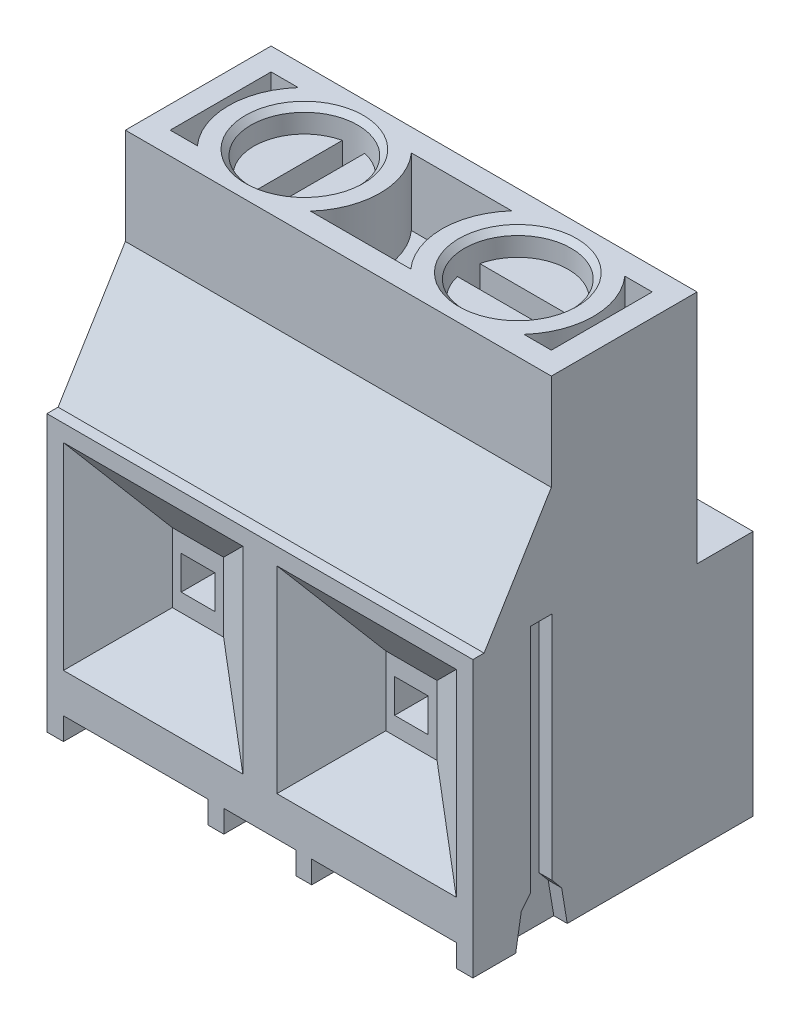
SolidWorks part; units mm, degrees
ref_plane "Front Plane" through (0, 0, 0) normal (0, 0, 1) x (1, 0, 0)
ref_plane "Top Plane" through (0, 0, 0) normal (0, 1, 0) x (1, 0, 0)
ref_plane "Right Plane" through (0, 0, 0) normal (1, 0, 0) x (0, 0, -1)
sketch "Sketch1" plane through (0, 0, 0) normal (1, 0, 0) x (0, 0, -1)
  line L0 (0, 0) -> (0, 12.3)
  line L1 (0, 12.3) -> (0.5, 12.3)
  line L2 (0.5, 12.3) -> (3.5, 17.2)
  line L3 (3.5, 17.2) -> (3.5, 21.5)
  line L4 (3.5, 21.5) -> (10, 21.5)
  line L5 (10, 21.5) -> (10, 11)
  line L6 (12.5, 0) -> (0, 0)
  line L8 (12.5, 0) -> (12.5, 11)
  line L9 (12.5, 11) -> (10, 11)
  dimension "D1" = 10
  dimension "D2" = 11
  dimension "D3" = 6.5
  dimension "D4" = 4.3
  dimension "D5" = 12.3
  dimension "D6" = 0.5
  dimension "D7" = 12.5
  dimension "D8" = 148.523
extrude "Boss-Extrude1" add sketch "Sketch1" along normal blind 19
sketch "Sketch2" plane through (0, 21.5, 0) normal (0, 1, 0) x (1, 0, 0)
  line L0 (-3.2112, 6.75) -> (22.2112, 6.75) construction
  line L1 (4.735, 11.5483) -> (4.735, 1.9517) construction
  line L2 (14.255, 11.5483) -> (14.255, 1.9517) construction
  line L3 (19, 10) -> (0, 10) construction
  line L4 (19, 3.5) -> (0, 3.5) construction
  line L5 (9.5, 11.5483) -> (9.5, 1.9517) construction
  line L6 (0, 10) -> (0, 3.5) construction
  line L7 (19, 10) -> (19, 3.5) construction
  line L12 (16.7773, 4.5) -> (18, 4.5)
  line L13 (11.7327, 9) -> (7.2573, 9)
  line L15 (7.2573, 4.5) -> (11.7327, 4.5)
  line L16 (1, 9) -> (1, 4.5)
  line L17 (1, 4.5) -> (18, 4.5)
  line L18 (18, 4.5) -> (18, 9)
  line L19 (18, 9) -> (1, 9)
  line L20 (1, 9) -> (1, 4.5)
  line L21 (1, 4.5) -> (2.2127, 4.5)
  line L22 (18, 4.5) -> (18, 9)
  line L23 (18, 9) -> (16.7773, 9)
  line L24 (2.2127, 9) -> (1, 9)
  circle A0 centre (4.735, 6.75) radius 2.38
  circle A1 centre (14.255, 6.75) radius 2.38
  arc A2 (2.2127, 9) -> (2.2127, 4.5) centre (4.735, 6.75) ccw
  arc A3 (11.7327, 9) -> (11.7327, 4.5) centre (14.255, 6.75) ccw
  circle A4 centre (4.735, 6.75) radius 3.38 construction
  circle A5 centre (14.255, 6.75) radius 3.38 construction
  arc A6 (7.2573, 4.5) -> (7.2573, 9) centre (4.735, 6.75) ccw
  arc A7 (16.7773, 4.5) -> (16.7773, 9) centre (14.255, 6.75) ccw
  point P3 (9.5, 6.75)
  point P6 (4.735, 6.75)
  point P9 (14.255, 6.75)
  point P16 (9.5, 6.75)
  dimension "D3" = 4.76
  dimension "D4" = 1
  dimension "D1" = 9.52
  dimension "D2" = 4.765
  dimension "D5" = 1
  dimension "D6" = 1
extrude "Cut-Extrude1" cut sketch "Sketch2" against normal blind 3
sketch "Sketch3" plane through (19, 0, 0) normal (1, 0, 0) x (0, 0, -1)
  line L0 (3.06, 0) -> (3.06, 6.7436) construction
  line L2 (0, 0) -> (12.5, 0) construction
  line L3 (1.91, 0) -> (2.16, 1.5)
  line L4 (2.16, 1.5) -> (2.58, 2)
  line L5 (2.58, 2) -> (2.58, 12.3)
  line L6 (2.58, 12.3) -> (3.54, 12.3)
  line L7 (1.91, 0) -> (4.21, 0)
  line L8 (0.5, 12.3) -> (0, 12.3) construction
  line L9 (0, 12.3) -> (0, 0) construction
  line L10 (3.54, 2) -> (3.54, 12.3)
  line L11 (3.96, 1.5) -> (3.54, 2)
  line L12 (4.21, 0) -> (3.96, 1.5)
  point P14 (3.06, 12.3)
  dimension "D1" = 1.15
  dimension "D2" = 0.9
  dimension "D3" = 0.48
  dimension "D4" = 2.58
  dimension "D5" = 1.5
  dimension "D6" = 0.5
extrude "Cut-Extrude2" cut sketch "Sketch3" against normal blind 0.6
sketch "Sketch4" plane through (0, 0, 0) normal (-1, 0, 0) x (0, 0, 1)
  line L0 (-1.91, 0) -> (-4.21, 0) construction
  line L1 (-3.54, 12.3) -> (-2.58, 12.3)
  line L2 (-3.54, 12.3) -> (-3.54, 0)
  line L3 (-3.54, 0) -> (-2.58, 0)
  line L4 (-2.58, 12.3) -> (-2.58, 0)
extrude "Boss-Extrude2" add sketch "Sketch4" along normal blind 0.6
chamfer "Chamfer1" distance 0.25 angle 45 2 edges at (4.735, 21.5, -4.37) (14.255, 21.5, -4.37)
sketch "Sketch6" plane through (0, 18.5, 0) normal (0, 1, 0) x (1, 0, 0)
  circle A0 centre (14.255, 6.75) radius 2.25
  circle A1 centre (4.735, 6.75) radius 2.25
  dimension "D1" = 4.5
extrude "Boss-Extrude3" add sketch "Sketch6" along normal blind 2 separate body
sketch "Sketch7" plane through (0, 20.5, 0) normal (0, 1, 0) x (1, 0, 0)
  line L2 (4.235, 8.9437) -> (4.235, 4.5563)
  line L4 (5.235, 8.9437) -> (5.235, 4.5563)
  line L7 (12.0613, 7.25) -> (16.4487, 7.25)
  line L9 (12.0613, 6.25) -> (16.4487, 6.25)
  circle A0 centre (4.735, 6.75) radius 2.25 construction
  circle A1 centre (14.255, 6.75) radius 2.25
  arc A2 (12.0613, 7.25) -> (12.0613, 6.25) centre (14.255, 6.75) ccw
  arc A3 (5.235, 8.9437) -> (4.235, 8.9437) centre (4.735, 6.75) ccw
  arc A5 (16.4487, 6.25) -> (16.4487, 7.25) centre (14.255, 6.75) ccw
  arc A6 (4.235, 4.5563) -> (5.235, 4.5563) centre (4.735, 6.75) ccw
  dimension "D1" = 0
extrude "Cut-Extrude3" cut sketch "Sketch7" against normal blind 1
sketch "Sketch8" plane through (0, 0, 0) normal (0, 0, 1) x (1, 0, 0)
  line L0 (4.74, 13.0511) -> (4.74, -1.0842) construction
  line L1 (9.5, 27.1864) -> (9.5, -1.0842) construction
  line L2 (14.26, 15.3842) -> (14.26, -1.0842) construction
  line L3 (0, 12.3) -> (0, 0) construction
  line L4 (19, 2) -> (19, 12.3) construction
  line L5 (19, 12.3) -> (0, 12.3) construction
  line L6 (10.26, 11.55) -> (18.26, 11.55)
  line L7 (10.26, 11.55) -> (10.26, 2.75)
  line L8 (10.26, 2.75) -> (18.26, 2.75)
  line L9 (18.26, 11.55) -> (18.26, 2.75)
  line L10 (10.26, 11.55) -> (18.26, 2.75) construction
  line L11 (10.26, 2.75) -> (18.26, 11.55) construction
  line L13 (0.74, 11.55) -> (8.74, 11.55)
  line L14 (0.74, 11.55) -> (0.74, 2.75)
  line L15 (0.74, 2.75) -> (8.74, 2.75)
  line L16 (8.74, 11.55) -> (8.74, 2.75)
  line L17 (0.74, 11.55) -> (8.74, 2.75) construction
  line L18 (0.74, 2.75) -> (8.74, 11.55) construction
  point P3 (4.74, 5.9835)
  point P6 (9.5, 13.0511)
  point P7 (14.26, 7.15)
  point P9 (15.9184, 13.0511)
  point P14 (14.26, 7.15)
  point P21 (4.74, 7.15)
  dimension "D1" = 9.52
  dimension "D2" = 4.76
  dimension "D3" = 8.8
  dimension "D4" = 8
  dimension "D5" = 0.75
  dimension "D6" = 8.8
  dimension "D7" = 8
extrude "Cut-Extrude4" cut sketch "Sketch8" against normal blind 2 draft 55
sketch "Sketch9" plane through (0, 0, -2) normal (0, 0, 1) x (1, 0, 0)
  line L1 (3.99, 7.9) -> (5.49, 7.9)
  line L2 (3.99, 7.9) -> (3.99, 6.4)
  line L3 (3.99, 6.4) -> (5.49, 6.4)
  line L4 (5.49, 7.9) -> (5.49, 6.4)
  line L5 (3.99, 7.9) -> (5.49, 6.4) construction
  line L6 (3.99, 6.4) -> (5.49, 7.9) construction
  line L7 (13.51, 7.9) -> (15.01, 7.9)
  line L8 (13.51, 7.9) -> (13.51, 6.4)
  line L9 (13.51, 6.4) -> (15.01, 6.4)
  line L10 (15.01, 7.9) -> (15.01, 6.4)
  line L11 (13.51, 7.9) -> (15.01, 6.4) construction
  line L12 (13.51, 6.4) -> (15.01, 7.9) construction
  point P0 (4.74, 7.15)
  point P5 (14.26, 7.15)
  dimension "D1" = 1.5
  dimension "D2" = 1.5
extrude "Cut-Extrude5" cut sketch "Sketch9" against normal blind 2
sketch "Sketch10" plane through (0, 0, 0) normal (0, 0, 1) x (1, 0, 0)
  line L0 (19, 0) -> (0, 0) construction
  line L1 (0.74, 0) -> (7.19, 0)
  line L2 (0.74, 0) -> (0.74, 1)
  line L3 (0.74, 1) -> (7.19, 1)
  line L4 (7.19, 0) -> (7.19, 1)
  line L6 (7.89, 1) -> (11.11, 1)
  line L7 (7.89, 1) -> (7.89, 0)
  line L8 (7.89, 0) -> (11.11, 0)
  line L9 (11.11, 1) -> (11.11, 0)
  line L10 (18.26, 1) -> (11.81, 1)
  line L11 (18.26, 1) -> (18.26, 0)
  line L12 (18.26, 0) -> (11.81, 0)
  line L13 (11.81, 1) -> (11.81, 0)
  dimension "D1" = 1
  dimension "D2" = 6.45
  dimension "D3" = 1
  dimension "D4" = 6.45
  dimension "D5" = 0.7
  dimension "D6" = 0.7
extrude "Cut-Extrude6" cut sketch "Sketch10" against normal through all
